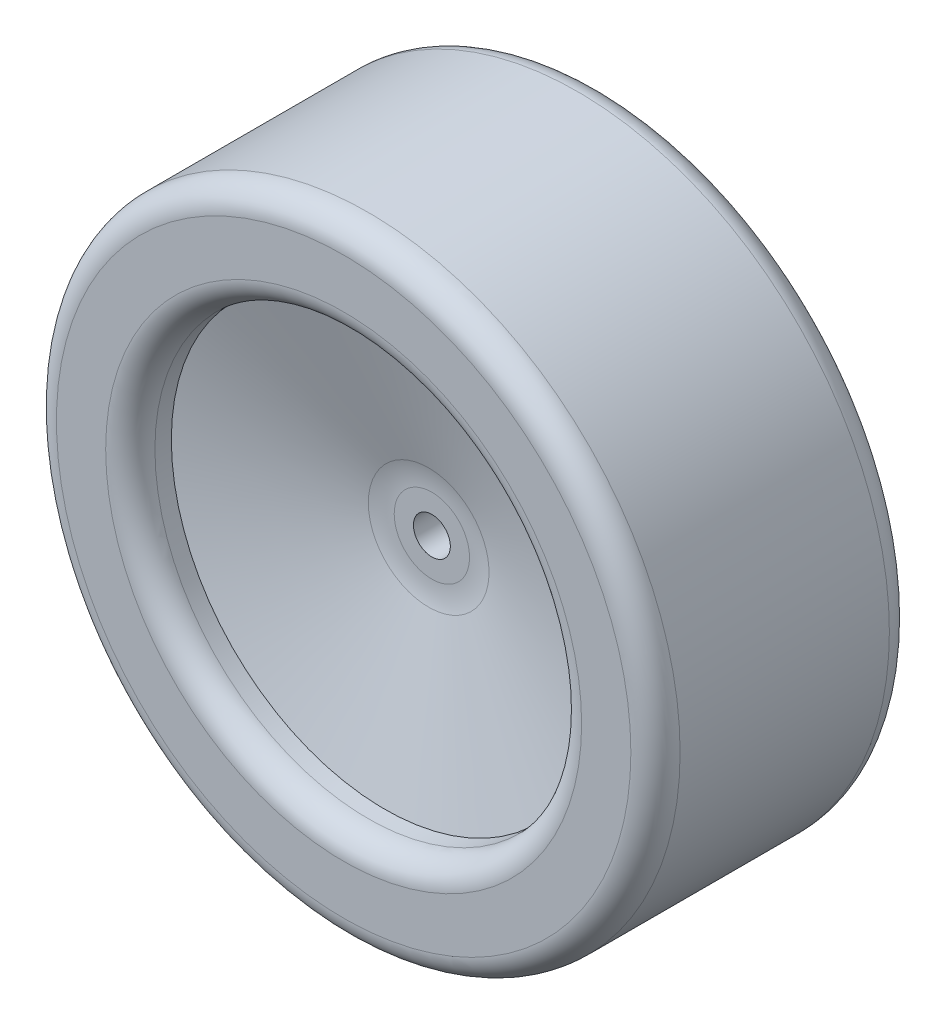
SolidWorks part; units mm, degrees
ref_plane "Alzado" through (0, 0, 0) normal (0, 0, 1) x (1, 0, 0)
ref_plane "Planta" through (0, 0, 0) normal (0, 1, 0) x (1, 0, 0)
ref_plane "Vista lateral" through (0, 0, 0) normal (1, 0, 0) x (0, 0, -1)
sketch "Croquis1" plane through (0, 0, 0) normal (1, 0, 0) x (0, 0, -1)
  line L1 (15.75, 38) -> (-15.75, 38)
  line L2 (-15.75, 38) -> (-15.75, 26)
  line L3 (-15.75, 26) -> (-10.75, 26)
  line L9 (-10.75, 26) -> (-5, 6)
  line L10 (5, 0) -> (-5, 0)
  line L11 (-5, 0) -> (-5, 6)
  line L14 (15.75, 38) -> (15.75, 26)
  line L15 (5, 0) -> (5, 6)
  line L16 (10.75, 26) -> (5, 6)
  line L17 (15.75, 26) -> (10.75, 26)
  line L18 (0, 0) -> (0, 38) construction
  point P1 (15.75, 32)
  point P4 (0, 0)
  point P5 (0, 0)
  dimension "D2" = 5
  dimension "D5" = 6
  dimension "D6" = 6
  dimension "D1" = 38
  dimension "D3" = 5
  dimension "D4" = 10
  dimension "D7" = 12
  dimension "D8" = 31.5
  dimension "D9" = 12
revolve "Revolución4" add sketch "Croquis1" angle 360 about L10
sketch "Croquis2" plane through (0, 0, -5) normal (0, 0, -1) x (-1, 0, 0)
  circle A0 centre (0, 0) radius 2.25
  dimension "D1" = 4.5
extrude "Cortar-Extruir1" cut sketch "Croquis2" against normal through all
fillet "Redondeo1" radius 3 4 edges at (-26, 0, -15.75) (-38, 0, -15.75) (-26, 0, 15.75) (-38, 0, 15.75)
fillet "Redondeo2" radius 10 2 edges at (-6, 0, -5) (-6, 0, 5)
